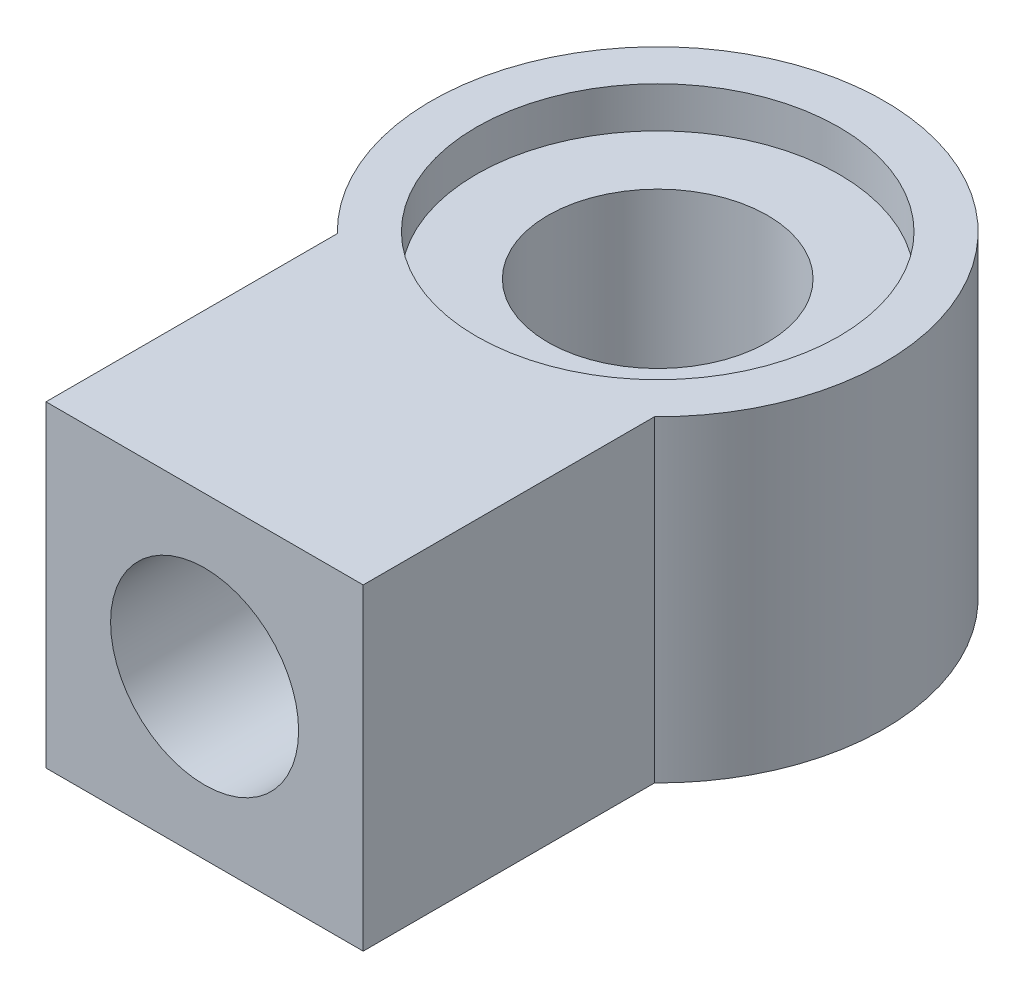
SolidWorks part; units mm, degrees
ref_plane "Front Plane" through (0, 0, 0) normal (0, 0, 1) x (1, 0, 0)
ref_plane "Top Plane" through (0, 0, 0) normal (0, 1, 0) x (1, 0, 0)
ref_plane "Right Plane" through (0, 0, 0) normal (1, 0, 0) x (0, 0, -1)
sketch "Sketch1" plane through (0, 0, 0) normal (0, 1, 0) x (1, 0, 0)
  circle A0 centre (0, 0) radius 5
  circle A1 centre (0, 0) radius 2.425
  dimension "D1" = 10
  dimension "D2" = 4.85
extrude "Boss-Extrude1" add sketch "Sketch1" along normal blind 7
ref_plane "Plane1" through (0, 0, 5) normal (0, 0, 1) x (1, 0, 0)
sketch "Sketch2" plane through (0, 0, 5) normal (0, 0, 1) x (1, 0, 0)
  line L0 (5, 7) -> (-5, 7) construction
  line L1 (3.5, 7) -> (-3.5, 7)
  line L2 (0, 7) -> (0, 0)
  line L3 (3.5, 0) -> (-3.5, 0)
  line L4 (-3.5, 7) -> (-3.5, 0)
  line L5 (-5, 0) -> (5, 0) construction
  line L6 (3.5, 7) -> (3.5, 0)
  dimension "D1" = 3.5
extrude "Boss-Extrude3" add sketch "Sketch2" against normal blind 1.5 contours L1 L4 L3 L2 | L6 L1 L2 L3
sketch "Sketch4" plane through (0, 0, 5) normal (0, 0, 1) x (1, 0, 0)
  line L1 (-3.5, 7) -> (3.5, 7)
  line L2 (-3.5, 7) -> (-3.5, 0)
  line L3 (-3.5, 0) -> (3.5, 0)
  line L4 (3.5, 7) -> (3.5, 0)
  circle A0 centre (0, 3.5) radius 2.075
  dimension "D1" = 4.15
extrude "Boss-Extrude4" add sketch "Sketch4" along normal blind 5
sketch "Sketch5" plane through (0, 7, 0) normal (0, 1, 0) x (1, 0, 0)
  circle A0 centre (0, 0) radius 4
  dimension "D1" = 8
extrude "Cut-Extrude1" cut sketch "Sketch5" against normal blind 0.9
